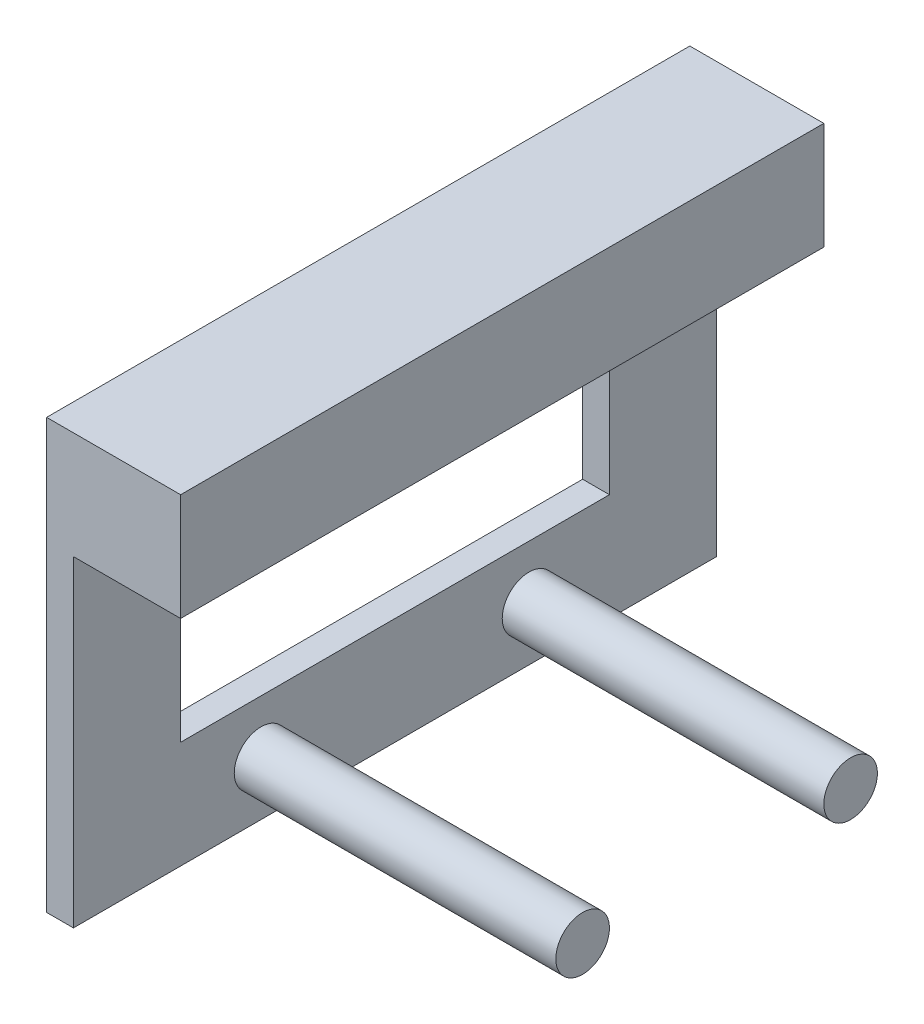
SolidWorks part; units mm, degrees
ref_plane "Front Plane" through (0, 0, 0) normal (0, 0, 1) x (1, 0, 0)
ref_plane "Top Plane" through (0, 0, 0) normal (0, 1, 0) x (1, 0, 0)
ref_plane "Right Plane" through (0, 0, 0) normal (1, 0, 0) x (0, 0, -1)
sketch "Sketch2" plane through (0, 0, 0) normal (1, 0, 0) x (0, 0, -1)
  line L0 (-40, 0) -> (40, 0)
  line L1 (40, 0) -> (40, 40)
  line L2 (40, 40) -> (-40, 40)
  line L3 (0, 269.6774) -> (0, -65.8065) construction
  line L4 (-40, 0) -> (-40, 40)
  point P8 (0, 0)
  point P9 (0, 40)
  dimension "D1" = 80
  dimension "D2" = 40
extrude "Boss-Extrude1" add sketch "Sketch2" along normal blind 7.5
sketch "Sketch3" plane through (7.5, 0, 0) normal (1, 0, 0) x (0, 0, -1)
  line L0 (-40, 18.5) -> (40, 18.5)
  line L1 (-40, 40) -> (-40, 0) construction
  line L2 (40, 0) -> (40, 40) construction
  line L3 (40, 18.5) -> (40, 0)
  line L4 (40, 0) -> (-40, 0)
  line L5 (-40, 0) -> (-40, 18.5)
  dimension "D1" = 18.5
extrude "Cut-Extrude1" cut sketch "Sketch3" against normal blind 5
sketch "Sketch9" plane through (7.5, 0, 0) normal (1, 0, 0) x (0, 0, -1)
  line L0 (-40, 40) -> (-40, 18.5) construction
  line L1 (-40, 35) -> (40, 35)
  line L2 (-40, 35) -> (-40, 18.5)
  line L3 (-40, 18.5) -> (40, 18.5)
  line L4 (40, 35) -> (40, 18.5)
  line L5 (40, 40) -> (-40, 40) construction
  dimension "D1" = 5
extrude "Cut-Extrude5" cut sketch "Sketch9" against normal blind 5
sketch "Sketch10" plane through (0, 0, 0) normal (-1, 0, 0) x (0, 0, 1)
  line L0 (40, 0) -> (-40, 0) construction
  line L1 (-40, 40) -> (-20, 40)
  line L2 (-40, 40) -> (-40, 0)
  line L3 (-40, 0) -> (-20, 0)
  line L4 (-20, 40) -> (-20, 0)
  line L5 (40, 40) -> (40, 0) construction
  dimension "D1" = 60
extrude "Cut-Extrude7" cut sketch "Sketch10" against normal blind 10
sketch "Sketch12" plane through (0, 0, 0) normal (-1, 0, 0) x (0, 0, 1)
  line L0 (-20, 40) -> (40, 40) construction
  line L1 (30, 10) -> (-10, 10)
  line L2 (30, 10) -> (30, 30)
  line L3 (30, 30) -> (-10, 30)
  line L4 (-10, 10) -> (-10, 30)
  line L5 (30, 10) -> (-10, 30) construction
  line L6 (30, 30) -> (-10, 10) construction
  line L7 (40, 0) -> (-20, 0) construction
  line L8 (-20, 0) -> (-20, 40) construction
  line L9 (40, 40) -> (40, 0) construction
  point P0 (10, 20)
  dimension "D1" = 10
  dimension "D2" = 10
  dimension "D3" = 10
  dimension "D4" = 10
extrude "Cut-Extrude8" cut sketch "Sketch12" against normal blind 10
sketch "Sketch13" plane through (2.5, 0, 0) normal (1, 0, 0) x (0, 0, -1)
  line L0 (20, 0) -> (20, 35) construction
  line L1 (-40, 35) -> (20, 35)
  line L2 (-40, 35) -> (-40, 30)
  line L3 (-40, 30) -> (20, 30)
  line L4 (20, 35) -> (20, 30)
extrude "Boss-Extrude5" add sketch "Sketch13" along normal blind 10
sketch "Sketch14" plane through (7.5, 0, 0) normal (1, 0, 0) x (0, 0, -1)
  line L1 (-40, 40) -> (20, 40)
  line L2 (-40, 40) -> (-40, 35)
  line L3 (-40, 35) -> (20, 35)
  line L4 (20, 40) -> (20, 35)
extrude "Boss-Extrude6" add sketch "Sketch14" along normal blind 5
sketch "Sketch15" plane through (2.5, 0, 0) normal (1, 0, 0) x (0, 0, -1)
  line L0 (-10, 10) -> (-10, 0) construction
  line L1 (10, 10) -> (-30, 10) construction
  line L2 (-40, 0) -> (20, 0) construction
  line L3 (-40, 5) -> (20, 5) construction
  line L4 (-40, 30) -> (-40, 0) construction
  line L5 (20, 0) -> (20, 30) construction
  circle A0 centre (-22.5, 5) radius 2.5
  circle A1 centre (2.5, 5) radius 2.5
  dimension "D1" = 5
  dimension "D2" = 25
extrude "Boss-Extrude7" add sketch "Sketch15" along normal blind 30
